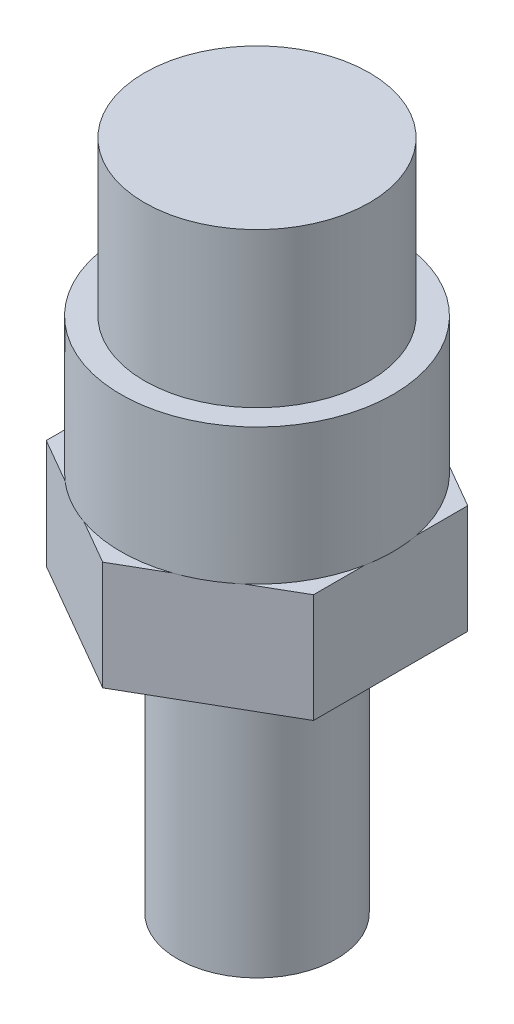
SolidWorks part; units mm, degrees
ref_plane "Front Plane" through (0, 0, 0) normal (0, 0, 1) x (1, 0, 0)
ref_plane "Top Plane" through (0, 0, 0) normal (0, 1, 0) x (1, 0, 0)
ref_plane "Right Plane" through (0, 0, 0) normal (1, 0, 0) x (0, 0, -1)
sketch "Sketch1" plane through (0, 0, 0) normal (0, 0, 1) x (1, 0, 0)
  line L0 (0, 0) -> (5.5563, 0)
  line L1 (5.5563, 0) -> (5.5563, 19.05)
  line L2 (5.5563, 19.05) -> (10.795, 19.05)
  line L3 (10.795, 19.05) -> (10.795, 26.67)
  line L4 (10.795, 26.67) -> (9.525, 26.67)
  line L5 (9.525, 26.67) -> (9.525, 36.195)
  line L6 (9.525, 36.195) -> (7.874, 36.195)
  line L7 (0, 46.99) -> (0, 0)
  line L8 (7.874, 36.195) -> (7.874, 46.99)
  line L9 (7.874, 46.99) -> (0, 46.99)
  dimension "D1" = 5.5562
  dimension "D2" = 19.05
  dimension "D3" = 9.525
  dimension "D4" = 10.795
  dimension "D5" = 7.874
  dimension "D6" = 7.62
  dimension "D7" = 27.94
  dimension "D8" = 9.525
revolve "Revolve1" add sketch "Sketch1" angle 360 about L7
sketch "Sketch2" plane through (0, 19.05, 0) normal (0, -1, 0) x (1, 0, 0)
  line L1 (0, 10.795) -> (-9.3487, 5.3975)
  line L2 (-9.3487, 5.3975) -> (-9.3487, -5.3975)
  line L3 (-9.3487, -5.3975) -> (0, -10.795)
  line L4 (0, -10.795) -> (9.3487, -5.3975)
  line L5 (9.3487, -5.3975) -> (9.3487, 5.3975)
  line L6 (9.3487, 5.3975) -> (0, 10.795)
  circle A0 centre (0, 0) radius 9.3487 construction
  circle A1 centre (0, 0) radius 10.795 construction
  circle A2 centre (0, 0) radius 10.795
  circle M1 centre (0, 0) radius 10.795
extrude "Cut-Extrude1" cut sketch "Sketch2" against normal up to surface (7.62 mm away) contours L1 M1 | L6 M1 | L5 M1 | L4 M1 | L3 M1 | L2 M1 up to face at (-9.525, 26.67, 0)
